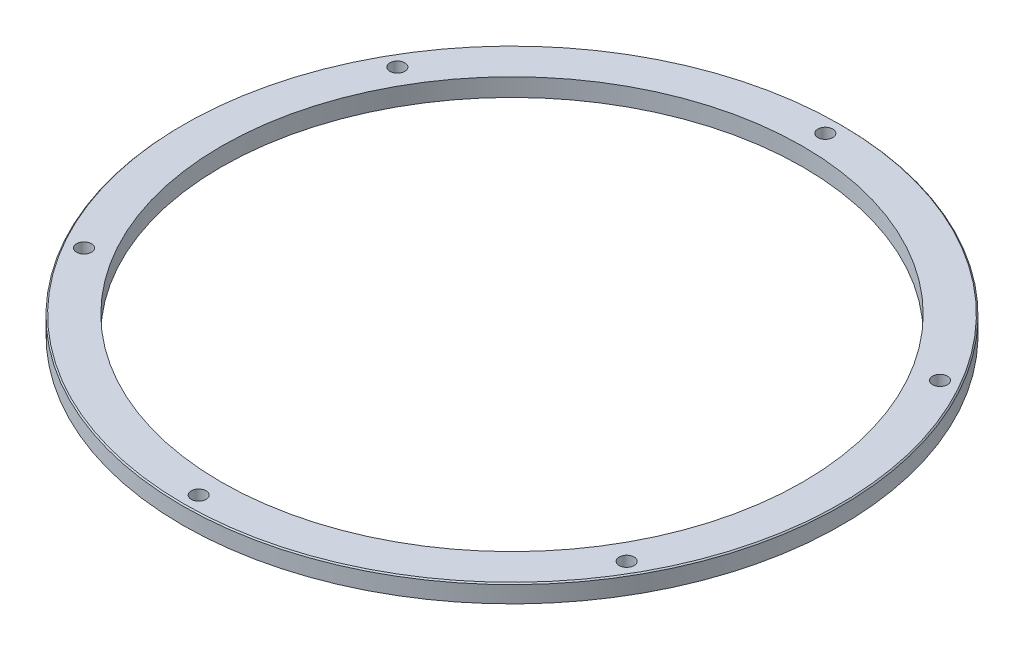
SolidWorks part; units mm, degrees
ref_plane "前视" through (0, 0, 0) normal (0, 0, 1) x (1, 0, 0)
ref_plane "上视" through (0, 0, 0) normal (0, 1, 0) x (1, 0, 0)
ref_plane "右视" through (0, 0, 0) normal (1, 0, 0) x (0, 0, -1)
sketch "草图1" plane through (0, 0, 0) normal (0, 1, 0) x (1, 0, 0)
  circle A0 centre (0, 0) radius 55.25
  circle A1 centre (0, 0) radius 48.75
  dimension "D1" = 6.5
  dimension "D2" = 110.5
extrude "凸台-拉伸1" add sketch "草图1" along normal blind 3
sketch "草图2" plane through (0, 3, 0) normal (0, 1, 0) x (1, 0, 0)
  line L0 (0, 0) -> (0, 52.525) construction
  circle A0 centre (0, 0) radius 52.525
  circle A1 centre (0, 52.525) radius 1.5
  circle A2 centre (45.488, 26.2625) radius 1.5
  circle A3 centre (45.488, -26.2625) radius 1.5
  circle A4 centre (0, -52.525) radius 1.5
  circle A5 centre (-45.488, -26.2625) radius 1.5
  circle A6 centre (-45.488, 26.2625) radius 1.5
  point P18 (0, 0)
  dimension "D1" = 6
hole_wizard "M3x0.5 螺纹孔1" positions "3D草图1" profile "草图3" tap size "M3x0.5" standard "ANSI Metric" end condition through all
sketch3d "3D草图1"
  point P0 (0, 3, -52.525)
  point P3 (45.488, 3, -26.2625)
  point P6 (45.488, 3, 26.2625)
  point P9 (0, 3, 52.525)
  point P12 (-45.488, 3, 26.2625)
  point P15 (-45.488, 3, -26.2625)
sketch "草图3" plane through (0, 3, -52.525) normal (1, 0, 0) x (0, 0, 1)
  line L0 (0, 0) -> (0, 3)
  line L1 (0, 3) -> (1.25, 3)
  line L2 (1.25, 3) -> (1.25, 0)
  line L5 (1.25, 0) -> (0, 0)
  line L11 (0, -6.35) -> (0, 107.95) construction
  dimension "通孔螺纹孔钻头直径" = 2.5
  dimension "通孔螺纹孔钻头深度" = 3
cosmetic thread "孔螺蚊线1" parameters "D2"=3
cosmetic thread "孔螺蚊线2" parameters "D2"=3
cosmetic thread "孔螺蚊线3" parameters "D2"=3
cosmetic thread "孔螺蚊线4" parameters "D2"=3
cosmetic thread "孔螺蚊线5" parameters "D2"=3
cosmetic thread "孔螺蚊线6" parameters "D2"=3
chamfer "倒角1" distance 0.2 angle 45 1 edges at (0, 3, 55.25)
